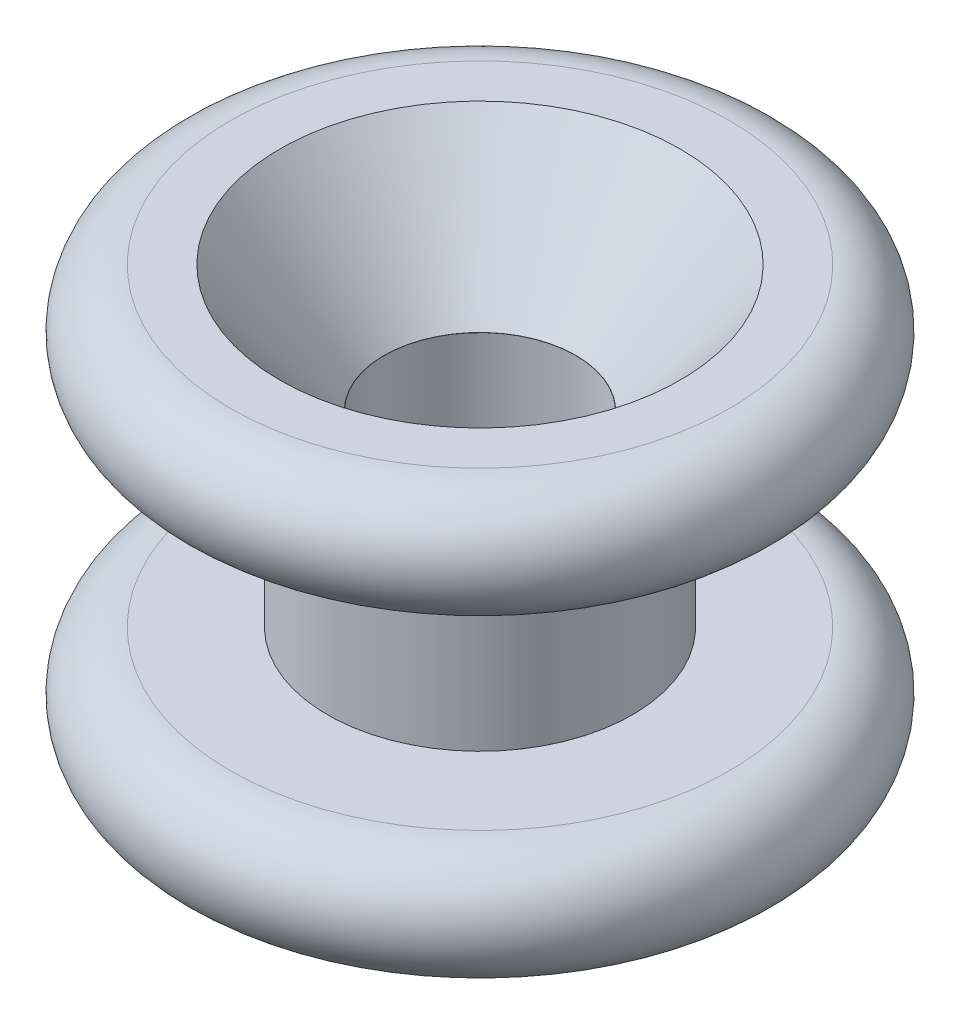
SolidWorks part; units mm, degrees
material "Delrin 2700 NC010, Low Viscosity Acetal Copolymer (SS)"
ref_plane "Front Plane" through (0, 0, 0) normal (0, 0, 1) x (1, 0, 0)
ref_plane "Top Plane" through (0, 0, 0) normal (0, 1, 0) x (1, 0, 0)
ref_plane "Right Plane" through (0, 0, 0) normal (1, 0, 0) x (0, 0, -1)
sketch "Sketch2" plane through (0, 0, 0) normal (0, 0, 1) x (1, 0, 0)
  line L0 (2.4968, -5.588) -> (2.4968, 5.588)
  line L1 (2.4968, 5.588) -> (6.5024, 5.588)
  line L2 (6.5024, 2.5908) -> (3.9751, 2.5908)
  line L3 (3.9751, 2.5908) -> (3.9751, -2.5908)
  line L4 (8.001, 4.0894) -> (8.001, 5.588) construction
  line L5 (0, 0) -> (3.9751, 0) construction
  line L6 (2.4968, -5.588) -> (6.5024, -5.588)
  line L7 (6.5024, -2.5908) -> (3.9751, -2.5908)
  line L8 (0, 0) -> (0, 5.588) construction
  arc A0 (6.5024, 5.588) -> (6.5024, 2.5908) centre (6.5024, 4.0894) cw
  arc A1 (6.5024, -5.588) -> (6.5024, -2.5908) centre (6.5024, -4.0894) ccw
  point P17 (2.4968, 0)
  dimension "D1" = 5.588
  dimension "D2" = 2.4968
  dimension "D3" = 3.9751
  dimension "D4" = 2.9972
  dimension "D5" = 8.001
revolve "Revolve1" add sketch "Sketch2" angle 360 about L8
sketch "Sketch3" plane through (0, 0, 0) normal (0, 0, 1) x (1, 0, 0)
  line L0 (0, 5.588) -> (5.2197, 5.588)
  line L1 (2.4968, 5.588) -> (-2.4968, 5.588) construction
  line L2 (6.5024, 5.588) -> (-6.5024, 5.588) construction
  line L3 (5.2197, 5.588) -> (2.5019, 2.286)
  line L4 (2.5019, 2.286) -> (0, 2.286)
  line L5 (0, 2.286) -> (0, 5.588)
  dimension "D1" = 5.2197
  dimension "D2" = 2.5019
  dimension "D3" = 3.302
revolve "Cut-Revolve1" cut sketch "Sketch3" angle 360 about L5
